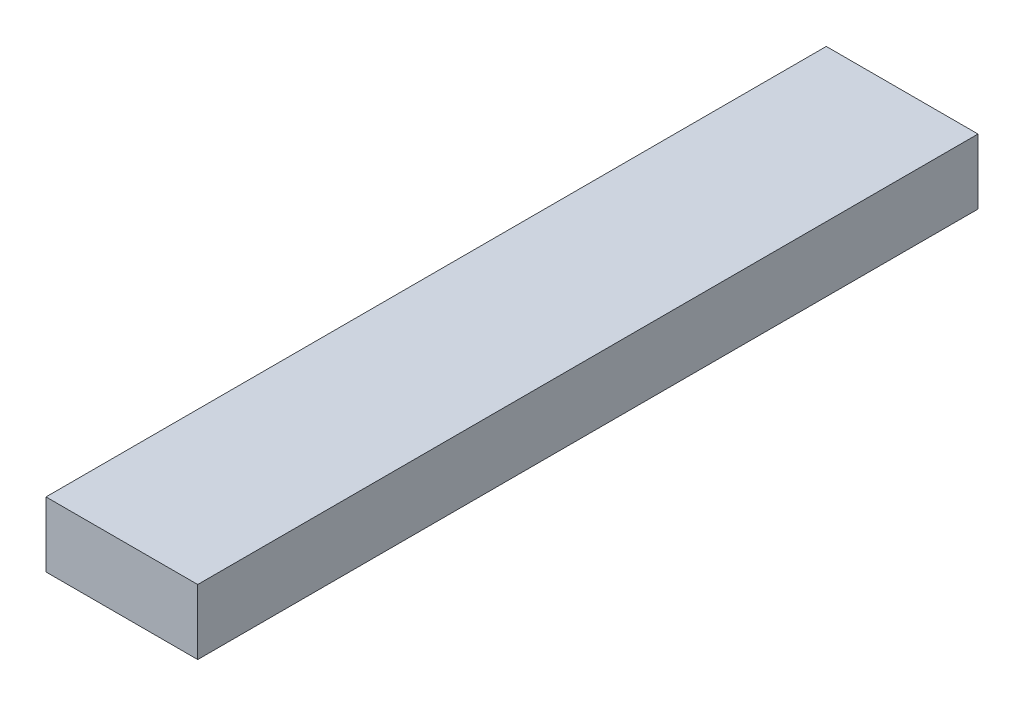
SolidWorks part; units mm, degrees
ref_plane "Front Plane" through (0, 0, 0) normal (0, 0, 1) x (1, 0, 0)
ref_plane "Top Plane" through (0, 0, 0) normal (0, 1, 0) x (1, 0, 0)
ref_plane "Right Plane" through (0, 0, 0) normal (1, 0, 0) x (0, 0, -1)
sketch "Sketch1" plane through (0, 0, 0) normal (0, 0, 1) x (1, 0, 0)
  line L1 (-7.9512, 26.3769) -> (80.9488, 26.3769)
  line L2 (-7.9512, 26.3769) -> (-7.9512, -11.7231)
  line L3 (-7.9512, -11.7231) -> (80.9488, -11.7231)
  line L4 (80.9488, 26.3769) -> (80.9488, -11.7231)
  dimension "D1" = 38.1
  dimension "D2" = 88.9
extrude "Boss-Extrude1" add sketch "Sketch1" along normal blind 457.2
